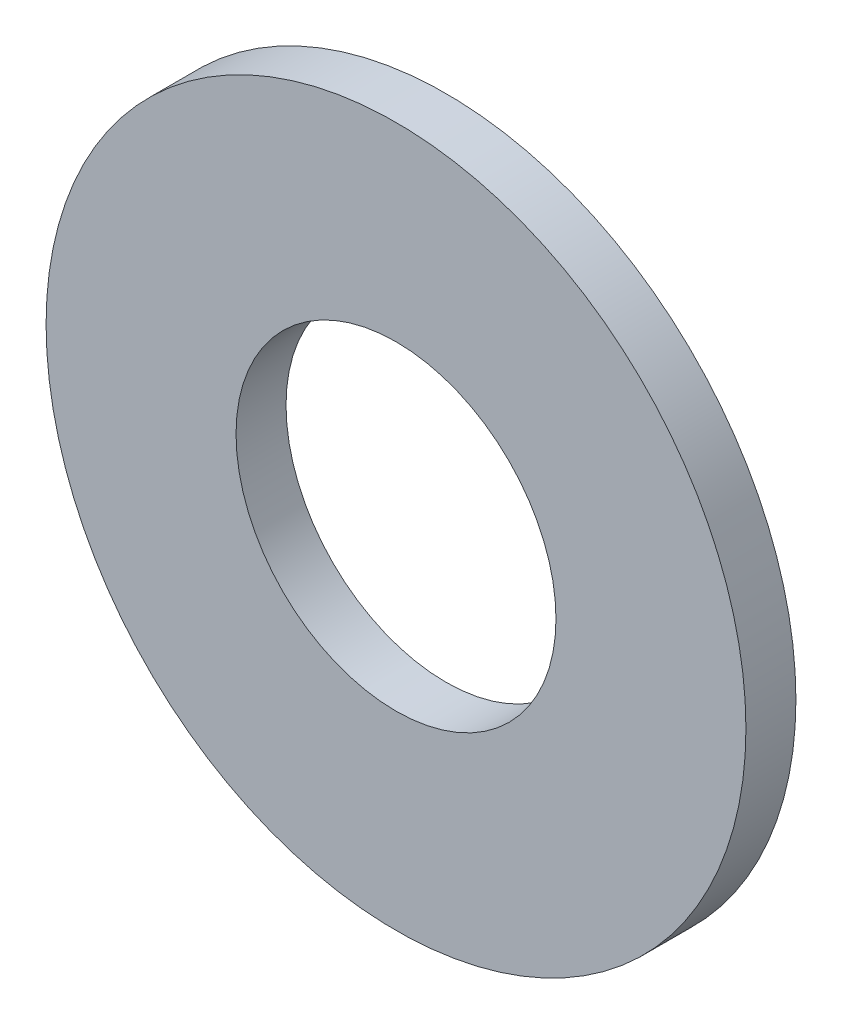
SolidWorks part; units mm, degrees
ref_plane "Front Plane" through (0, 0, 0) normal (0, 0, 1) x (1, 0, 0)
ref_plane "Top Plane" through (0, 0, 0) normal (0, 1, 0) x (1, 0, 0)
ref_plane "Right Plane" through (0, 0, 0) normal (1, 0, 0) x (0, 0, -1)
sketch "Sketch1" plane through (0, 0, 0) normal (0, 0, 1) x (1, 0, 0)
  circle A0 centre (0, 0) radius 3.5
  circle A1 centre (0, 0) radius 1.6
  dimension "D1" = 7
  dimension "D2" = 3.2
extrude "Boss-Extrude1" add sketch "Sketch1" along normal blind 0.5
